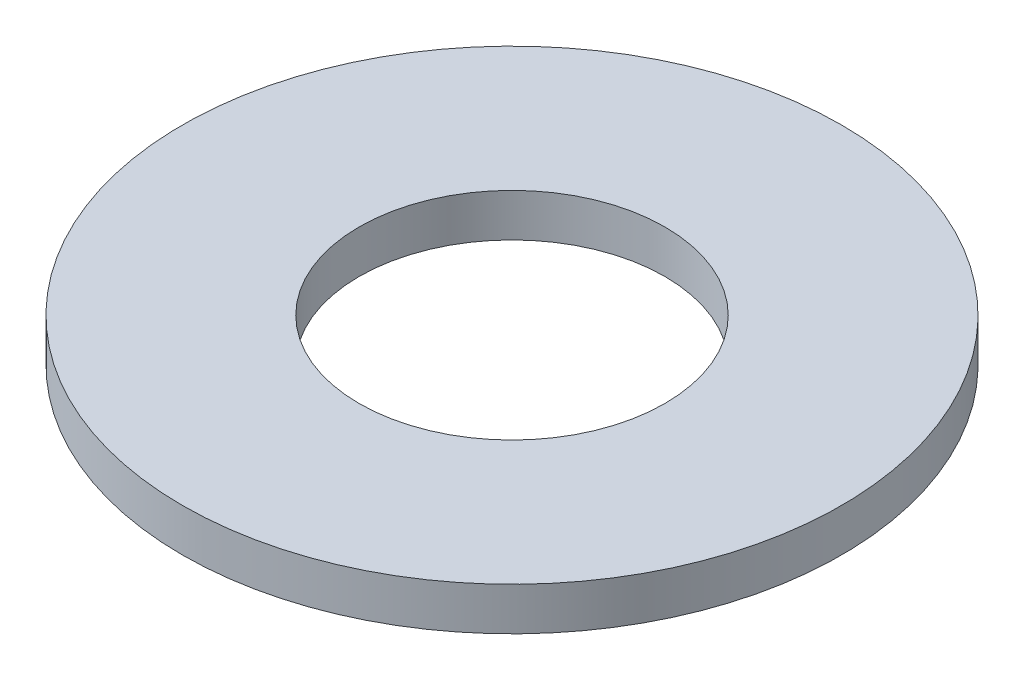
SolidWorks part; units mm, degrees
material "AISI 316 Stainless Steel Sheet (SS)"
ref_plane "Front Plane" through (0, 0, 0) normal (0, 0, 1) x (1, 0, 0)
ref_plane "Top Plane" through (0, 0, 0) normal (0, 1, 0) x (1, 0, 0)
ref_plane "Right Plane" through (0, 0, 0) normal (1, 0, 0) x (0, 0, -1)
sketch "Sketch1" plane through (0, 0, 0) normal (0, 1, 0) x (1, 0, 0)
  circle A0 centre (0, 0) radius 11.1125
  dimension "OD" = 22.225
extrude "Boss-Extrude1" add sketch "Sketch1" along normal blind 1.4478
sketch "Sketch5" plane through (0, 1.4478, 0) normal (0, 1, 0) x (-1, 0, 0)
  circle A0 centre (0, 0) radius 5.1562
  dimension "ID" = 10.3124
extrude "Cut-Extrude1" cut sketch "Sketch5" against normal through all
